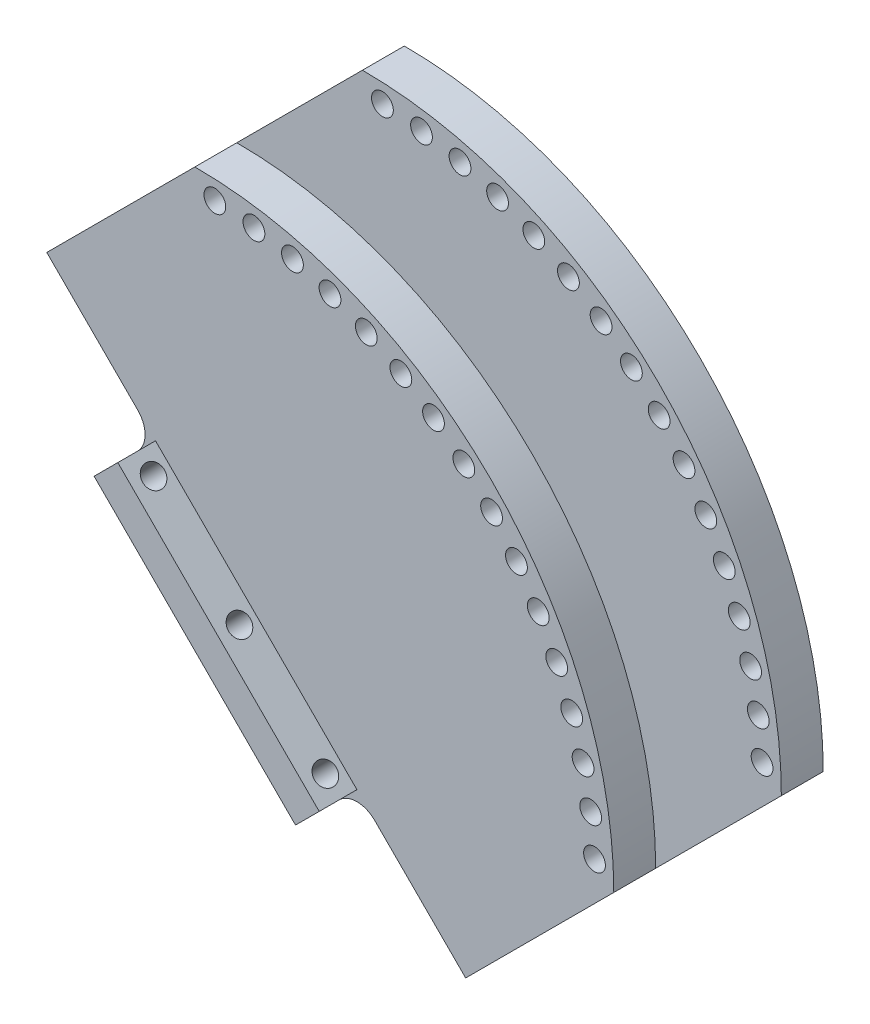
SolidWorks part; units mm, degrees
ref_plane "Front Plane" through (0, 0, 0) normal (0, 0, 1) x (1, 0, 0)
ref_plane "Top Plane" through (0, 0, 0) normal (0, 1, 0) x (1, 0, 0)
ref_plane "Right Plane" through (0, 0, 0) normal (1, 0, 0) x (0, 0, -1)
sketch "Sketch1" plane through (0, 0, 0) normal (0, 0, 1) x (1, 0, 0)
  line L2 (0, 0) -> (47.7, 2.3) construction
  line L3 (0, 50) -> (-17.6777, 32.3223)
  line L4 (-17.6777, 32.3223) -> (32.3223, -17.6777)
  line L5 (50, 0) -> (32.3223, -17.6777)
  arc A0 (0, 50) -> (50, 0) centre (0, 0) cw
  circle A1 centre (47.7, 2.3) radius 1.3
  circle A112 centre (2.3865, 47.6958) radius 1.3
  circle A113 centre (7.05, 47.2322) radius 1.3
  circle A114 centre (11.6456, 46.3137) radius 1.3
  circle A115 centre (16.1291, 44.9492) radius 1.3
  circle A116 centre (20.4572, 43.1519) radius 1.3
  circle A120 centre (24.5883, 40.9389) radius 1.3
  circle A121 centre (28.4826, 38.3317) radius 1.3
  circle A122 centre (32.1026, 35.3553) radius 1.3
  circle A123 centre (35.4135, 32.0385) radius 1.3
  circle A124 centre (38.3833, 28.4131) radius 1.3
  circle A125 centre (40.9834, 24.514) radius 1.3
  circle A126 centre (43.1889, 20.3789) radius 1.3
  circle A127 centre (44.9784, 16.0475) radius 1.3
  circle A128 centre (46.3348, 11.5616) radius 1.3
  circle A129 centre (47.2449, 6.9643) radius 1.3
  circle A134 centre (-11.5616, 46.3348) radius 1.3 [skipped]
  circle A135 centre (-32.0385, 35.4135) radius 1.3 [skipped]
  circle A136 centre (-24.514, 40.9834) radius 1.3 [skipped]
  circle A137 centre (-20.3789, 43.1889) radius 1.3 [skipped]
  circle A138 centre (-16.0475, 44.9784) radius 1.3 [skipped]
  circle A139 centre (-28.4131, 38.3833) radius 1.3 [skipped]
  circle A140 centre (-35.3553, 32.1026) radius 1.3 [skipped]
  circle A141 centre (-38.3317, 28.4826) radius 1.3 [skipped]
  circle A142 centre (-47.7, -2.3) radius 1.3 [skipped]
  circle A143 centre (-40.9389, 24.5883) radius 1.3 [skipped]
  circle A144 centre (-47.6958, 2.3865) radius 1.3 [skipped]
  circle A145 centre (-46.3348, -11.5616) radius 1.3 [skipped]
  circle A146 centre (-47.2449, -6.9643) radius 1.3 [skipped]
  circle A147 centre (-35.4135, -32.0385) radius 1.3 [skipped]
  circle A148 centre (-32.1026, -35.3553) radius 1.3 [skipped]
  circle A149 centre (32.0385, -35.4135) radius 1.3 [skipped]
  circle A150 centre (35.3553, -32.1026) radius 1.3 [skipped]
  circle A151 centre (38.3317, -28.4826) radius 1.3 [skipped]
  circle A152 centre (40.9389, -24.5883) radius 1.3 [skipped]
  circle A153 centre (43.1519, -20.4572) radius 1.3 [skipped]
  circle A154 centre (44.9492, -16.1291) radius 1.3 [skipped]
  circle A155 centre (28.4131, -38.3833) radius 1.3 [skipped]
  circle A156 centre (24.514, -40.9834) radius 1.3 [skipped]
  circle A157 centre (20.3789, -43.1889) radius 1.3 [skipped]
  circle A158 centre (16.0475, -44.9784) radius 1.3 [skipped]
  circle A159 centre (11.5616, -46.3348) radius 1.3 [skipped]
  circle A160 centre (6.9643, -47.2449) radius 1.3 [skipped]
  circle A161 centre (2.3, -47.7) radius 1.3 [skipped]
  circle A162 centre (-2.3865, -47.6958) radius 1.3 [skipped]
  circle A163 centre (-7.05, -47.2322) radius 1.3 [skipped]
  circle A164 centre (-11.6456, -46.3137) radius 1.3 [skipped]
  circle A165 centre (-16.1291, -44.9492) radius 1.3 [skipped]
  circle A166 centre (-20.4572, -43.1519) radius 1.3 [skipped]
  circle A167 centre (-24.5883, -40.9389) radius 1.3 [skipped]
  circle A168 centre (-28.4826, -38.3317) radius 1.3 [skipped]
  circle A169 centre (-38.3833, -28.4131) radius 1.3 [skipped]
  circle A170 centre (-40.9834, -24.514) radius 1.3 [skipped]
  circle A171 centre (-43.1889, -20.3789) radius 1.3 [skipped]
  circle A172 centre (-47.2322, 7.05) radius 1.3 [skipped]
  circle A173 centre (-46.3137, 11.6456) radius 1.3 [skipped]
  circle A174 centre (-44.9492, 16.1291) radius 1.3 [skipped]
  circle A175 centre (-43.1519, 20.4572) radius 1.3 [skipped]
  circle A176 centre (-2.3, 47.7) radius 1.3 [skipped]
  circle A177 centre (-6.9643, 47.2449) radius 1.3 [skipped]
  circle A178 centre (-44.9784, -16.0475) radius 1.3 [skipped]
  circle A179 centre (46.3137, -11.6456) radius 1.3 [skipped]
  circle A180 centre (47.2322, -7.05) radius 1.3 [skipped]
  circle A181 centre (47.6958, -2.3865) radius 1.3 [skipped]
  dimension "D3" = 2.6
  dimension "D4" = 47.7
  dimension "D1" = 25
  dimension "D2" = 50
  dimension "D6" = 70.7107
  dimension "D9" = 47.7554
  dimension "D5" = 25
  dimension "D8" = 64
extrude "Boss-Extrude1" add sketch "Sketch1" along normal blind 5
ref_plane "Plane1" through (7.3223, 7.3223, 0) normal (-0.7071, -0.7071, 0) x (-0.7071, 0.7071, 0)
sketch "Sketch3" plane through (7.3223, 7.3223, 0) normal (-0.7071, -0.7071, 0) x (-0.7071, 0.7071, 0)
  line L5 (0, 0.7) -> (0, 3.3) construction
  line L11 (17, -12.5) -> (17, 4.5)
  line L12 (17, 4.5) -> (-17, 4.5)
  line L13 (-17, 4.5) -> (-17, -12.5)
  line L14 (-17, -12.5) -> (17, -12.5)
  line L15 (17, -5) -> (-17, -5) construction
  line L16 (35.3553, -5) -> (-35.3553, -5) construction
  line L17 (-35.3553, 0) -> (35.3553, 0) construction
  circle A0 centre (0, 2) radius 1.3
  circle A1 centre (14.5, 2) radius 1.3
  circle A2 centre (-14.5, 2) radius 1.3
  point P5 (0, 0)
  dimension "D1" = 2.6
  dimension "D10" = 17
  dimension "D2" = 2.5
  dimension "D4" = 2.5
  dimension "D5" = 2.5
  dimension "D6" = 7.5
  dimension "D7" = 17
  dimension "D8" = 34
  dimension "D9" = 2.5
  dimension "D3" = 2
extrude "Boss-Extrude2" add sketch "Sketch3" along normal blind 4
ref_plane "Plane2" through (0, 0, 12.5) normal (0, 0, 1) x (1, 0, 0)
mirror "Mirror1" about plane through (0, 0, 12.5) normal (0, 0, 1) of "Boss-Extrude1", "Boss-Extrude2"
mirror "Mirror2" about plane through (0, 0, 12.5) normal (0, 0, 1) of "Boss-Extrude1"
fillet "Fillet1" radius 3 1 edges at (19.3431, -4.6985, 22.5)
fillet "Fillet2" radius 3 3 edges at (-4.6985, 19.3431, 2.5) (-4.6985, 19.3431, 22.5) (19.3431, -4.6985, 2.5)
